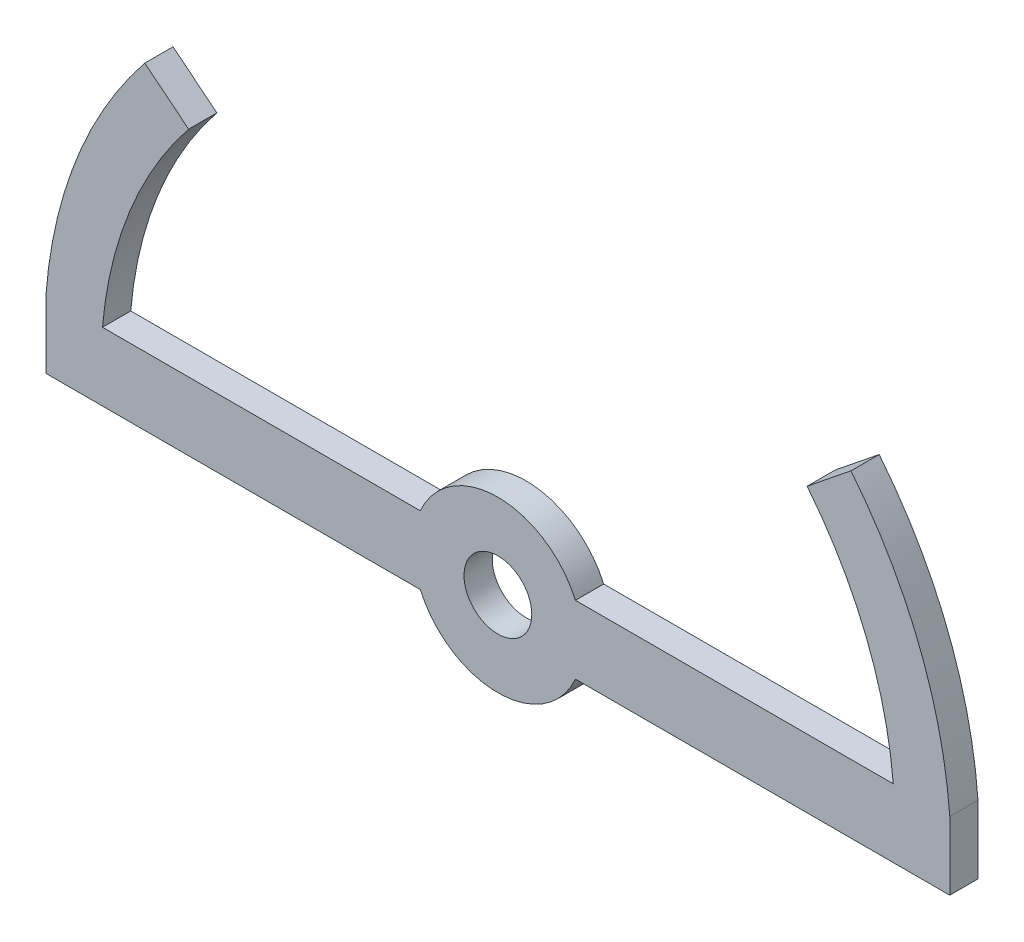
SolidWorks part; units mm, degrees
ref_plane "Front Plane" through (0, 0, 0) normal (0, 0, 1) x (1, 0, 0)
ref_plane "Top Plane" through (0, 0, 0) normal (0, 1, 0) x (1, 0, 0)
ref_plane "Right Plane" through (0, 0, 0) normal (1, 0, 0) x (0, 0, -1)
sketch "Sketch1" plane through (0, 0, 0) normal (0, 0, 1) x (1, 0, 0)
  circle A1 centre (0, 0) radius 7.5
  circle A3 centre (0, 0) radius 3
extrude "Boss-Extrude1" add sketch "Sketch1" against normal offset from surface (2.5 mm away) 0.5
sketch "Sketch2" plane through (0, 0, -2.5) normal (0, 0, -1) x (-1, 0, 0)
  line L1 (-40, -3.0199) -> (40, -3.0199)
  line L2 (-40, -3.0199) -> (-40, 3.0199)
  line L3 (-40, 3.0199) -> (40, 3.0199)
  line L4 (40, -3.0199) -> (40, 3.0199)
  line L5 (0, 3.0199) -> (0, -3.0199) construction
  line L6 (-40, 0) -> (40, 0) construction
  circle A0 centre (0, 0) radius 3 construction
  circle A1 centre (0, 0) radius 3
  point P0 (0, 0)
  dimension "D1" = 80
  dimension "D2" = 6.0398
extrude "Boss-Extrude2" add sketch "Sketch2" against normal up to surface (2.5 mm away) up to face at (3, 0, 0)
sketch "Sketch4" plane through (0, 0, -2.5) normal (0, 0, -1) x (-1, 0, 0)
  line L0 (40, 3.0199) -> (6.8651, 3.0199) construction
  line L1 (27.3723, 22.0199) -> (31.2555, 25.1438)
  line L2 (40, 3.0199) -> (35, 3.0199)
  line L3 (0, 0) -> (0, 18.3588) construction
  line L4 (-27.3723, 22.0199) -> (-31.2555, 25.1438)
  line L5 (-40, 3.0199) -> (-35, 3.0199)
  arc A0 (40, 3.0199) -> (31.2555, 25.1438) centre (0, 0) ccw
  arc A1 (35, 3.0199) -> (27.3723, 22.0199) centre (0, 0) ccw
  arc A2 (-40, 3.0199) -> (-31.2555, 25.1438) centre (0, 0) cw
  arc A3 (-35, 3.0199) -> (-27.3723, 22.0199) centre (0, 0) cw
  dimension "D1" = 5
  dimension "D2" = 19
extrude "Boss-Extrude3" add sketch "Sketch4" against normal up to surface (2.5 mm away) up to face at (0, 0, 0)
